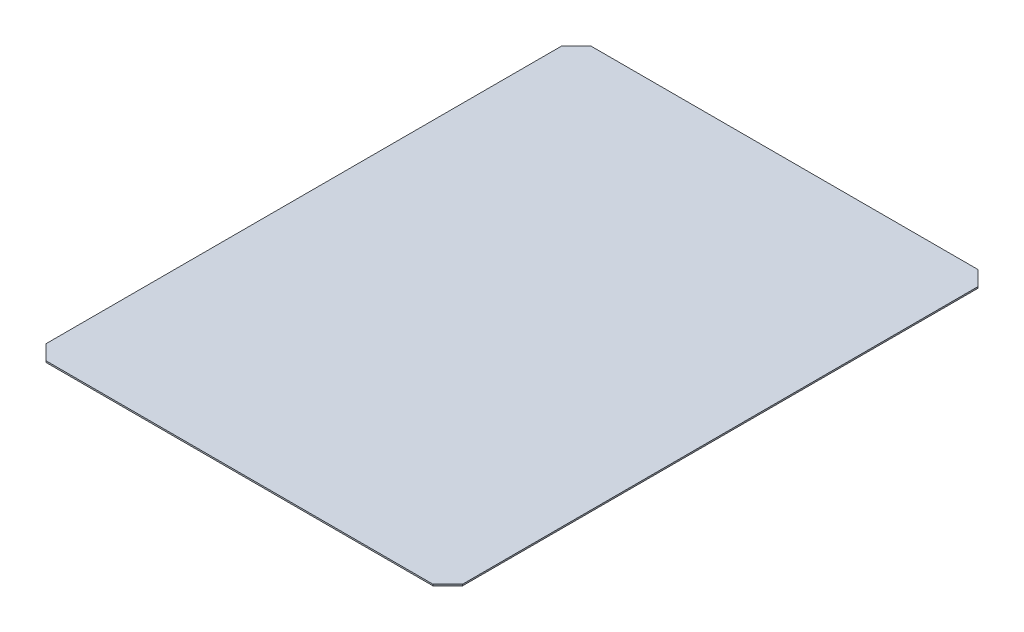
SolidWorks part; units mm, degrees
ref_plane "Plan de face" through (0, 0, 0) normal (0, 0, 1) x (1, 0, 0)
ref_plane "Plan de dessus" through (0, 0, 0) normal (0, 1, 0) x (1, 0, 0)
ref_plane "Plan de droite" through (0, 0, 0) normal (1, 0, 0) x (0, 0, -1)
sketch "Esquisse1" plane through (0, 0, 0) normal (0, 1, 0) x (1, 0, 0)
  line L1 (0, 0) -> (3100, 0)
  line L2 (0, 0) -> (0, 3690)
  line L3 (0, 3690) -> (3100, 3690)
  line L4 (3100, 0) -> (3100, 3690)
  dimension "D1" = 3690
  dimension "D2" = 3100
extrude "Boss.-Extru.1" add sketch "Esquisse1" along normal blind 10
sketch "Esquisse2" plane through (0, 0, 0) normal (0, 0, 1) x (1, 0, 0)
  line L0 (0, 0) -> (3100, 0) construction
  line L1 (0, 10) -> (140, 10)
  line L2 (0, 10) -> (0, 0)
  line L3 (0, 0) -> (140, 0)
  line L4 (140, 10) -> (140, 0)
  line L6 (3100, 10) -> (2960, 10)
  line L7 (3100, 10) -> (3100, 0)
  line L8 (3100, 0) -> (2960, 0)
  line L9 (2960, 10) -> (2960, 0)
  dimension "D1" = 140
  dimension "D2" = 140
extrude "Enlèv. mat.-Extru.1" cut sketch "Esquisse2" against normal blind 3980.6
chamfer "Chanfrein1" distance 100 angle 45 4 edges at (140, 5, -3690) (2960, 5, -3690) (2960, 5, 0) (140, 5, 0)
